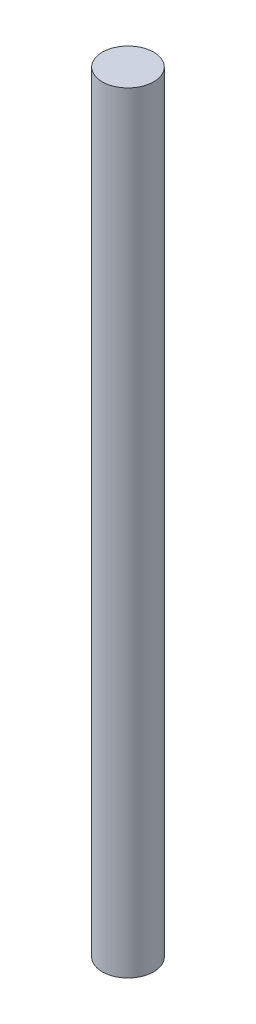
SolidWorks part; units mm, degrees
ref_plane "Front Plane" through (0, 0, 0) normal (0, 0, 1) x (1, 0, 0)
ref_plane "Top Plane" through (0, 0, 0) normal (0, 1, 0) x (1, 0, 0)
ref_plane "Right Plane" through (0, 0, 0) normal (1, 0, 0) x (0, 0, -1)
sketch "Sketch1" plane through (0, 0, 0) normal (0, 1, 0) x (1, 0, 0)
  circle A0 centre (0, 0) radius 50
  dimension "D1" = 100
extrude "Boss-Extrude1" add sketch "Sketch1" against normal blind 1500
